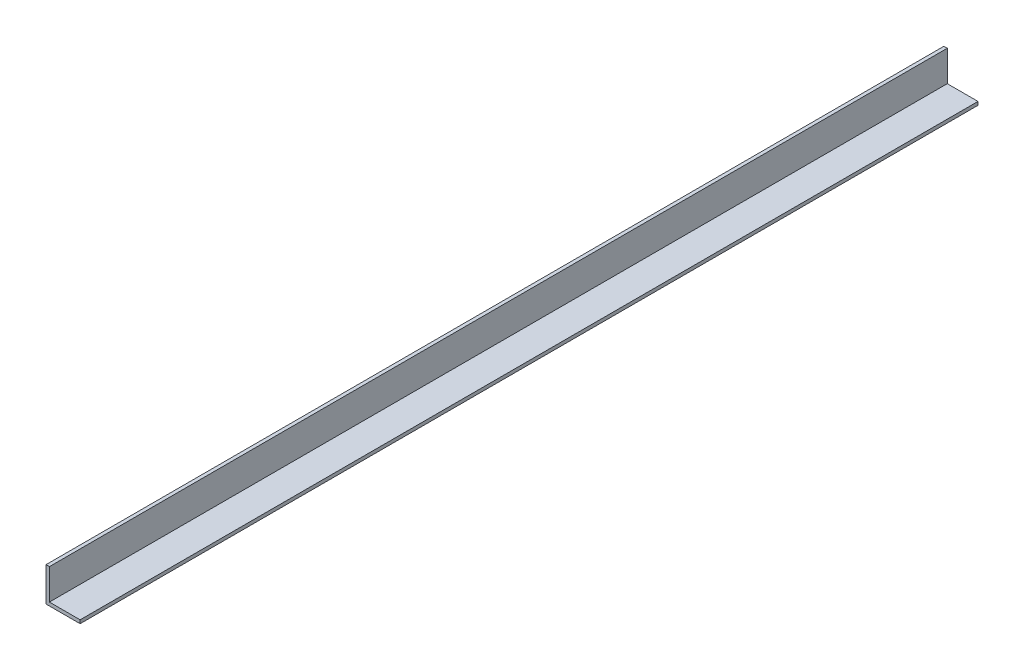
SolidWorks part; units mm, degrees
material "6063 T5"
ref_plane "Спереди" through (0, 0, 0) normal (0, 0, 1) x (1, 0, 0)
ref_plane "Сверху" through (0, 0, 0) normal (0, 1, 0) x (1, 0, 0)
ref_plane "Справа" through (0, 0, 0) normal (1, 0, 0) x (0, 0, -1)
sketch "Эскиз1" plane through (0, 0, 0) normal (0, 0, 1) x (1, 0, 0)
  line L0 (0, 38) -> (0, 0)
  line L1 (0, 0) -> (38, 0)
  line L2 (38, 0) -> (38, 3.8)
  line L3 (38, 3.8) -> (3.8, 3.8)
  line L4 (3.8, 3.8) -> (3.8, 38)
  line L5 (3.8, 38) -> (0, 38)
  dimension "D1" = 38
  dimension "D2" = 3.8
extrude "Бобышка-Вытянуть1" add sketch "Эскиз1" along normal blind 1000
